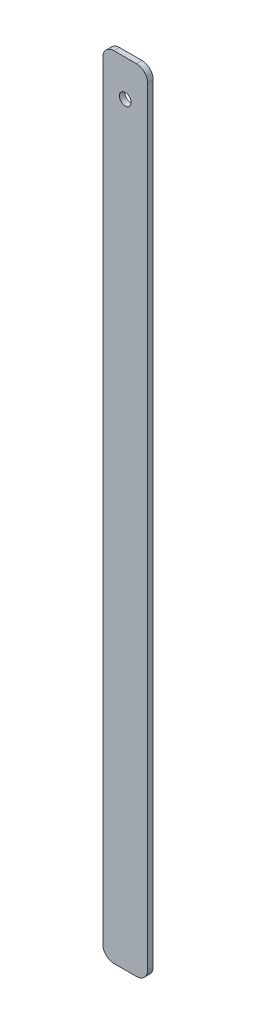
SolidWorks part; units mm, degrees
material "6061-T6 (SS)"
ref_plane "Front Plane" through (0, 0, 0) normal (0, 0, 1) x (1, 0, 0)
ref_plane "Top Plane" through (0, 0, 0) normal (0, 1, 0) x (1, 0, 0)
ref_plane "Right Plane" through (0, 0, 0) normal (1, 0, 0) x (0, 0, -1)
sketch "Sketch2" plane through (0, 0, 0) normal (0, 0, 1) x (1, 0, 0)
  line L11 (0, 0) -> (8, 0)
  line L12 (0, 0) -> (0, 141.2)
  line L13 (0, 141.2) -> (8, 141.2)
  line L14 (8, 0) -> (8, 141.2)
  circle A7 centre (4, 134.7) radius 1.05
  dimension "D1" = 8
  dimension "D3" = 2.1
  dimension "D2" = 141.2
  dimension "D4" = 6.5
  dimension "D5" = 4
extrude "Boss-Extrude1" add sketch "Sketch2" along normal blind 1
fillet "Fillet1" radius 2 4 edges at (0, 141.2, 0.5) (8, 141.2, 0.5) (8, 0, 0.5) (0, 0, 0.5)
sketch "Sketch3" plane through (0, 0, 1) normal (0, 0, 1) x (1, 0, 0)
  line L2 (2, 0) -> (6, 0) construction
  line L5 (0, 139.2) -> (0, 2) construction
  circle A0 centre (4, 3.92) radius 1.651
  dimension "D1" = 3.302
  dimension "D2" = 3.92
  dimension "D3" = 4
